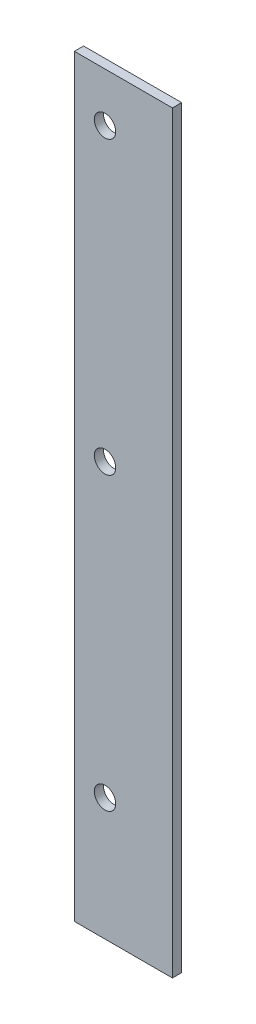
SolidWorks part; units mm, degrees
ref_plane "Front Plane" through (0, 0, 0) normal (0, 0, 1) x (1, 0, 0)
ref_plane "Top Plane" through (0, 0, 0) normal (0, 1, 0) x (1, 0, 0)
ref_plane "Right Plane" through (0, 0, 0) normal (1, 0, 0) x (0, 0, -1)
sketch "Sketch1" plane through (0, 0, 0) normal (0, 0, 1) x (1, 0, 0)
  line L5 (0, 0) -> (16, 0)
  line L6 (0, 0) -> (0, 123)
  line L7 (0, 123) -> (16, 123)
  line L8 (16, 0) -> (16, 123)
  dimension "D1" = 123
  dimension "D2" = 16
extrude "Boss-Extrude1" add sketch "Sketch1" along normal blind 1.5
sketch "Sketch2" plane through (0, 0, 1.5) normal (0, 0, 1) x (1, 0, 0)
  line L0 (0, 0) -> (16, 0) construction
  line L1 (0, 123) -> (0, 0) construction
  circle A0 centre (5, 20) radius 1.75
  dimension "D1" = 20
  dimension "D2" = 5
  dimension "D3" = 3.5
extrude "Cut-Extrude1" cut sketch "Sketch2" against normal through all
pattern_linear "LPattern1" count 3 spacing 47.5 along (0, 1, 0) of "Cut-Extrude1"
